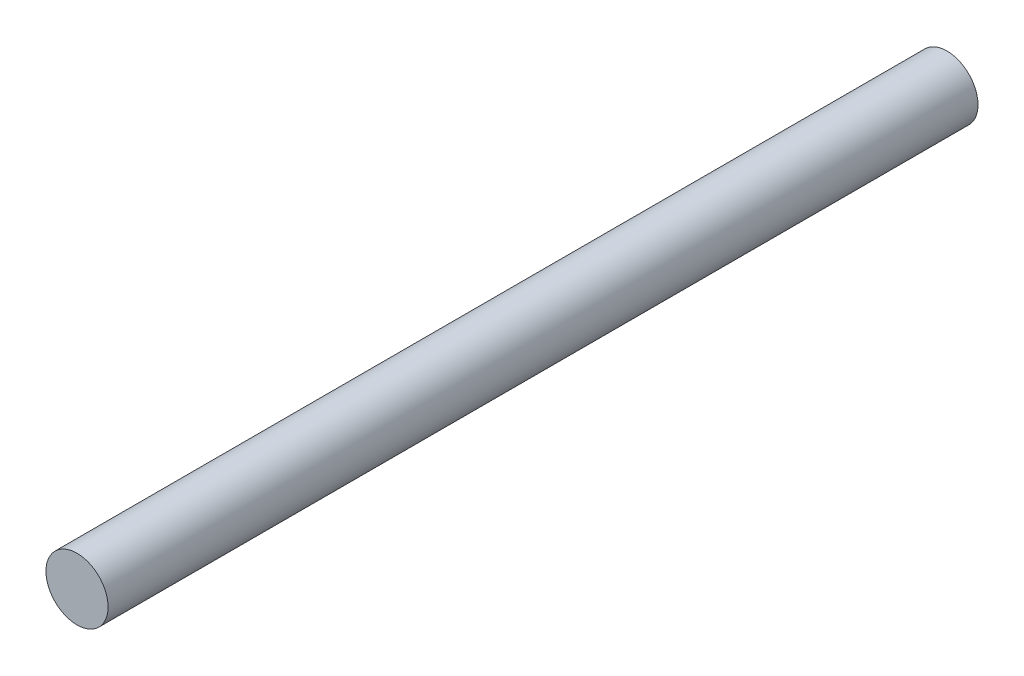
SolidWorks part; units mm, degrees
material "Alloy Steel"
ref_plane "Front Plane" through (0, 0, 0) normal (0, 0, 1) x (1, 0, 0)
ref_plane "Top Plane" through (0, 0, 0) normal (0, 1, 0) x (1, 0, 0)
ref_plane "Right Plane" through (0, 0, 0) normal (1, 0, 0) x (0, 0, -1)
sketch "Sketch1" plane through (0, 0, 0) normal (0, 0, 1) x (1, 0, 0)
  circle A0 centre (0, 0) radius 3
  dimension "D1" = 6
extrude "Boss-Extrude1" add sketch "Sketch1" along normal blind 84
